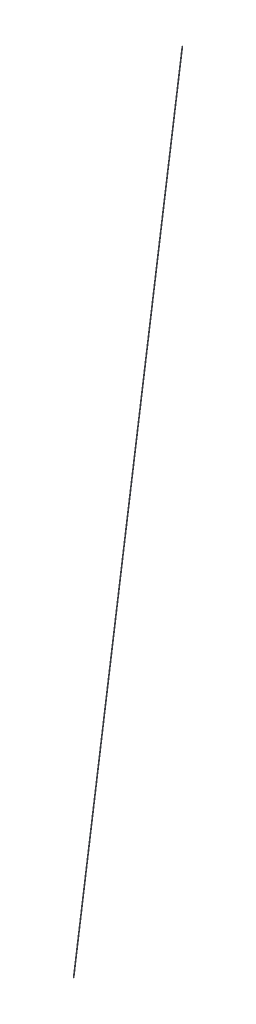
SolidWorks part; units mm, degrees
ref_plane "前视基准面" through (0, 0, 0) normal (0, 0, 1) x (1, 0, 0)
ref_plane "上视基准面" through (0, 0, 0) normal (0, 1, 0) x (1, 0, 0)
ref_plane "右视基准面" through (0, 0, 0) normal (1, 0, 0) x (0, 0, -1)
sketch "草图1" plane through (0, 0, 0) normal (0, 1, 0) x (1, 0, 0)
  line L0 (0, 0) -> (0, -217.5)
sketch "草图2" plane through (0, 0, 0) normal (0, 0, 1) x (1, 0, 0)
  line L0 (0, 0) -> (0, 500)
sketch "草图3" plane through (0, 0, 0) normal (1, 0, 0) x (0, 0, -1)
  line L4 (0, 0) -> (-217.5, 0) construction
  line L8 (0, 1505) -> (-217.5, 0)
sweep "扫描1" add path "草图3" circular profile diameter 1 parameters "D3"=1
